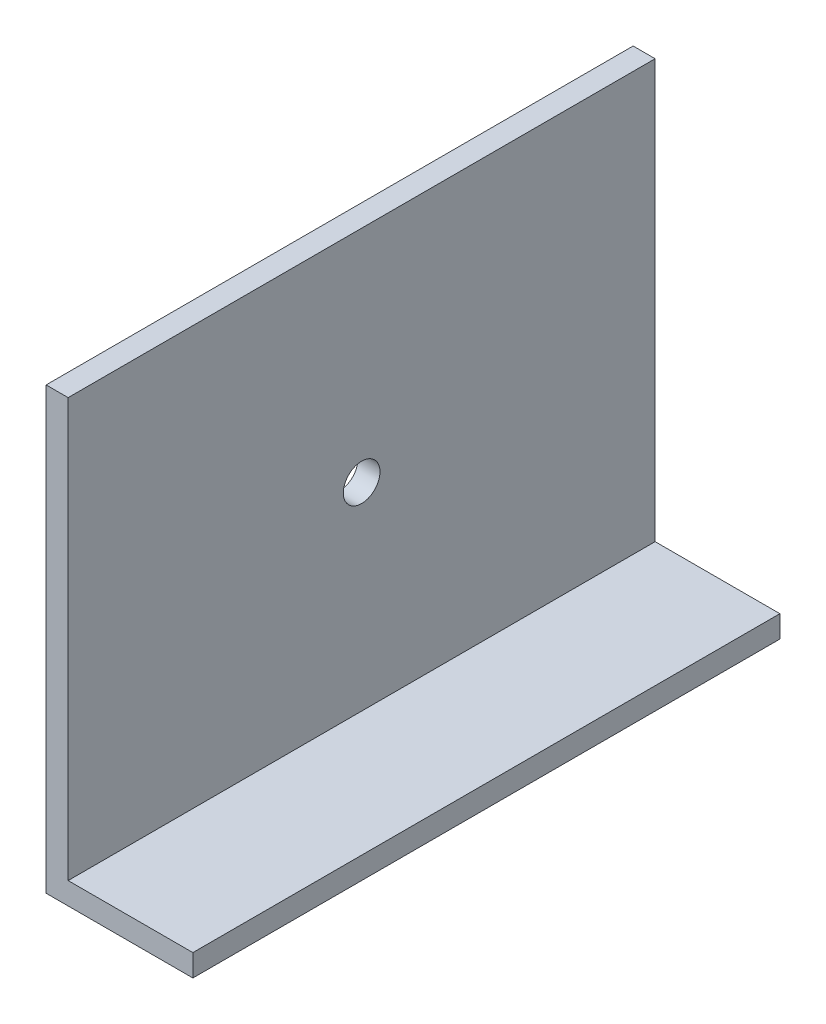
SolidWorks part; units mm, degrees
ref_plane "Front Plane" through (0, 0, 0) normal (0, 0, 1) x (1, 0, 0)
ref_plane "Top Plane" through (0, 0, 0) normal (0, 1, 0) x (1, 0, 0)
ref_plane "Right Plane" through (0, 0, 0) normal (1, 0, 0) x (0, 0, -1)
sketch "Sketch1" plane through (0, 0, 0) normal (0, 0, 1) x (1, 0, 0)
  line L1 (0, 0) -> (20, 0)
  line L2 (0, 0) -> (0, 60)
  line L3 (0, 60) -> (3, 60)
  line L4 (20, 0) -> (20, 3)
  line L7 (20, 3) -> (3, 3)
  line L8 (3, 60) -> (3, 3)
  dimension "D1" = 60
  dimension "D2" = 20
  dimension "D3" = 3
  dimension "D4" = 3
extrude "Boss-Extrude1" add sketch "Sketch1" along normal blind 80
sketch "Sketch2" plane through (0, 0, 0) normal (-1, 0, 0) x (0, 0, 1)
  line L0 (80, 0) -> (0, 0) construction
  circle A0 centre (40, 30) radius 2.5
  point P4 (0, 0)
  point P5 (0, 0)
  point P6 (40, 0)
  dimension "D2" = 5
  dimension "D1" = 30
extrude "Cut-Extrude1" cut sketch "Sketch2" against normal through all
